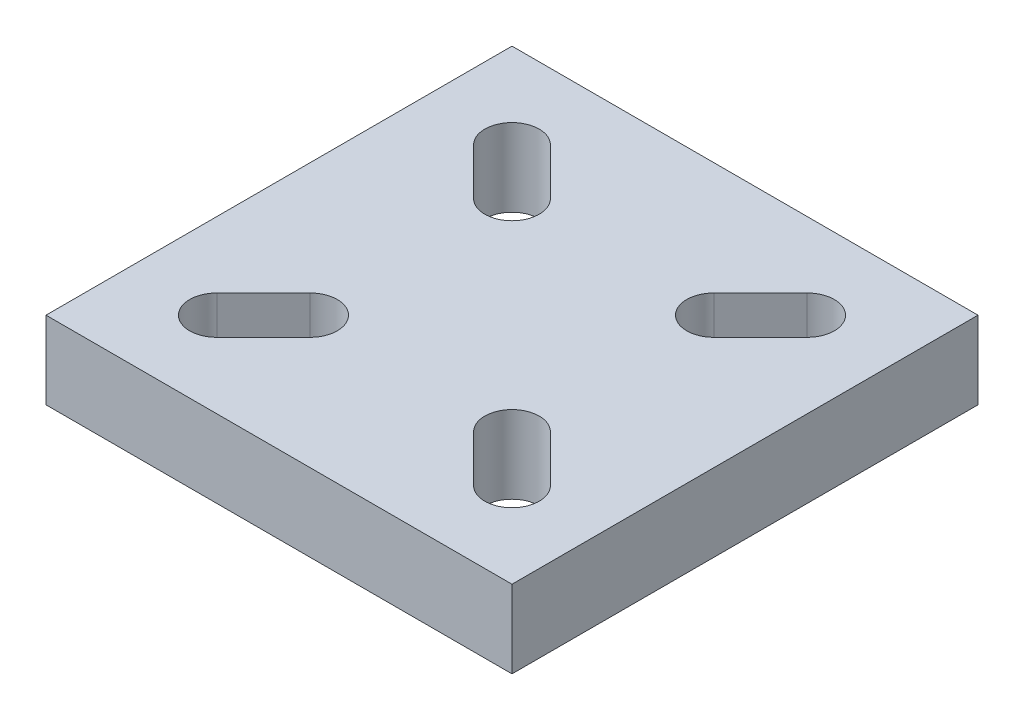
SolidWorks part; units mm, degrees
ref_plane "Front Plane" through (0, 0, 0) normal (0, 0, 1) x (1, 0, 0)
ref_plane "Top Plane" through (0, 0, 0) normal (0, 1, 0) x (1, 0, 0)
ref_plane "Right Plane" through (0, 0, 0) normal (1, 0, 0) x (0, 0, -1)
sketch "Sketch1" plane through (0, 0, 0) normal (0, 1, 0) x (1, 0, 0)
  line L1 (30, 30) -> (-30, 30)
  line L2 (30, 30) -> (30, -30)
  line L3 (30, -30) -> (-30, -30)
  line L4 (-30, 30) -> (-30, -30)
  line L5 (30, 30) -> (-30, -30) construction
  line L6 (30, -30) -> (-30, 30) construction
  point P0 (0, 0)
  dimension "D1" = 60
  dimension "D2" = 60
extrude "Boss-Extrude1" add sketch "Sketch1" along normal blind 10 contours L1 L4 L3 L2
sketch "Sketch2" plane through (0, 10, 0) normal (0, 1, 0) x (1, 0, 0)
  point P0 (55, 55)
  point P1 (55, -55)
  point P2 (-55, -55)
  point P3 (-55, 55)
  point P4 (0, 0)
  dimension "D1" = 110
  dimension "D2" = 55
  dimension "D3" = 55
  dimension "D4" = 55
sketch "Sketch4" plane through (0, 10, 0) normal (0, 1, 0) x (1, 0, 0)
  line L0 (-19, 19) -> (-13, 13) construction
  line L1 (-16.5251, 21.4749) -> (-10.5251, 15.4749)
  line L2 (-21.4749, 16.5251) -> (-15.4749, 10.5251)
  line L3 (19, 19) -> (13, 13) construction
  line L4 (21.4749, 16.5251) -> (15.4749, 10.5251)
  line L5 (16.5251, 21.4749) -> (10.5251, 15.4749)
  line L6 (19, -19) -> (13, -13) construction
  line L7 (16.5251, -21.4749) -> (10.5251, -15.4749)
  line L8 (21.4749, -16.5251) -> (15.4749, -10.5251)
  line L9 (-19, -19) -> (-13, -13) construction
  line L10 (-21.4749, -16.5251) -> (-15.4749, -10.5251)
  line L11 (-16.5251, -21.4749) -> (-10.5251, -15.4749)
  line L12 (-13, 13) -> (-31.1907, 13) construction
  arc A0 (-16.5251, 21.4749) -> (-21.4749, 16.5251) centre (-19, 19) ccw
  arc A1 (-15.4749, 10.5251) -> (-10.5251, 15.4749) centre (-13, 13) ccw
  arc A2 (21.4749, 16.5251) -> (16.5251, 21.4749) centre (19, 19) ccw
  arc A3 (10.5251, 15.4749) -> (15.4749, 10.5251) centre (13, 13) ccw
  arc A4 (16.5251, -21.4749) -> (21.4749, -16.5251) centre (19, -19) ccw
  arc A5 (15.4749, -10.5251) -> (10.5251, -15.4749) centre (13, -13) ccw
  arc A6 (-21.4749, -16.5251) -> (-16.5251, -21.4749) centre (-19, -19) ccw
  arc A7 (-10.5251, -15.4749) -> (-15.4749, -10.5251) centre (-13, -13) ccw
  point P2 (-16, 16)
  point P10 (-27.628, -19.5221)
  point P13 (16, 16)
  point P20 (16, -16)
  point P27 (-16, -16)
  point P32 (0, 0)
  point P33 (0, 0)
  dimension "D2" = 3.5
  dimension "D1" = 19
  dimension "D3" = 13
  dimension "D5" = 45
  dimension "D4" = 4
extrude "Cut-Extrude1" cut sketch "Sketch4" against normal through all
equation "\"D3@Sketch2\"=\"D1@Sketch2\"/2"
equation "\"D2@Sketch2\"=\"D1@Sketch2\"/2"
equation "\"D4@Sketch2\"=\"D3@Sketch2\""
